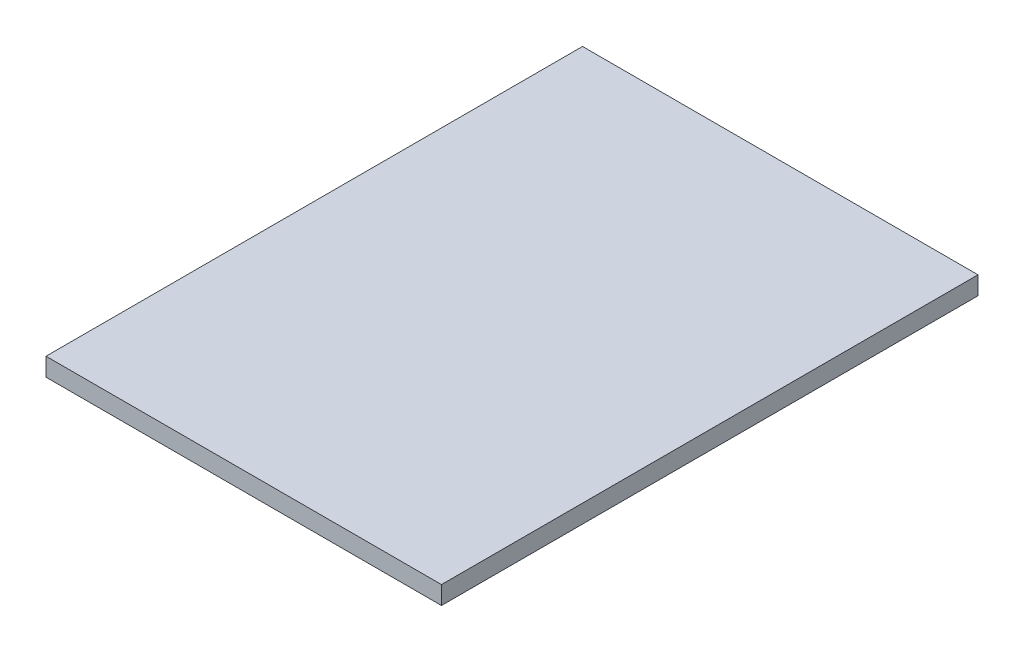
SolidWorks part; units mm, degrees
ref_plane "Front Plane" through (0, 0, 0) normal (0, 0, 1) x (1, 0, 0)
ref_plane "Top Plane" through (0, 0, 0) normal (0, 1, 0) x (1, 0, 0)
ref_plane "Right Plane" through (0, 0, 0) normal (1, 0, 0) x (0, 0, -1)
sketch "Sketch1" plane through (0, 0, 0) normal (0, 1, 0) x (1, 0, 0)
  line L1 (-32.6341, -44.2721) -> (32.6341, -44.2721)
  line L2 (-32.6341, -44.2721) -> (-32.6341, 44.2721)
  line L3 (-32.6341, 44.2721) -> (32.6341, 44.2721)
  line L4 (32.6341, -44.2721) -> (32.6341, 44.2721)
  line L5 (-32.6341, -44.2721) -> (32.6341, 44.2721) construction
  line L6 (-32.6341, 44.2721) -> (32.6341, -44.2721) construction
  point P0 (0, 0)
  dimension "D1" = 110
extrude "Boss-Extrude1" add sketch "Sketch1" along normal blind 3
